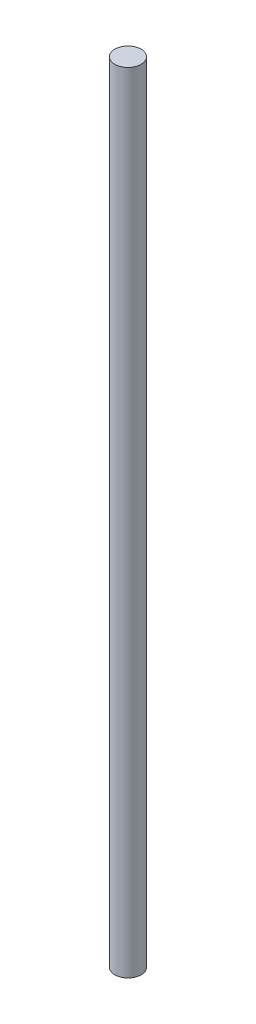
SolidWorks part; units mm, degrees
ref_plane "Front Plane" through (0, 0, 0) normal (0, 0, 1) x (1, 0, 0)
ref_plane "Top Plane" through (0, 0, 0) normal (0, 1, 0) x (1, 0, 0)
ref_plane "Right Plane" through (0, 0, 0) normal (1, 0, 0) x (0, 0, -1)
sketch "Sketch1" plane through (0, 0, 0) normal (0, 1, 0) x (1, 0, 0)
  circle A0 centre (0, 0) radius 4
  dimension "D1" = 8
extrude "Boss-Extrude1" add sketch "Sketch1" along normal blind 240
